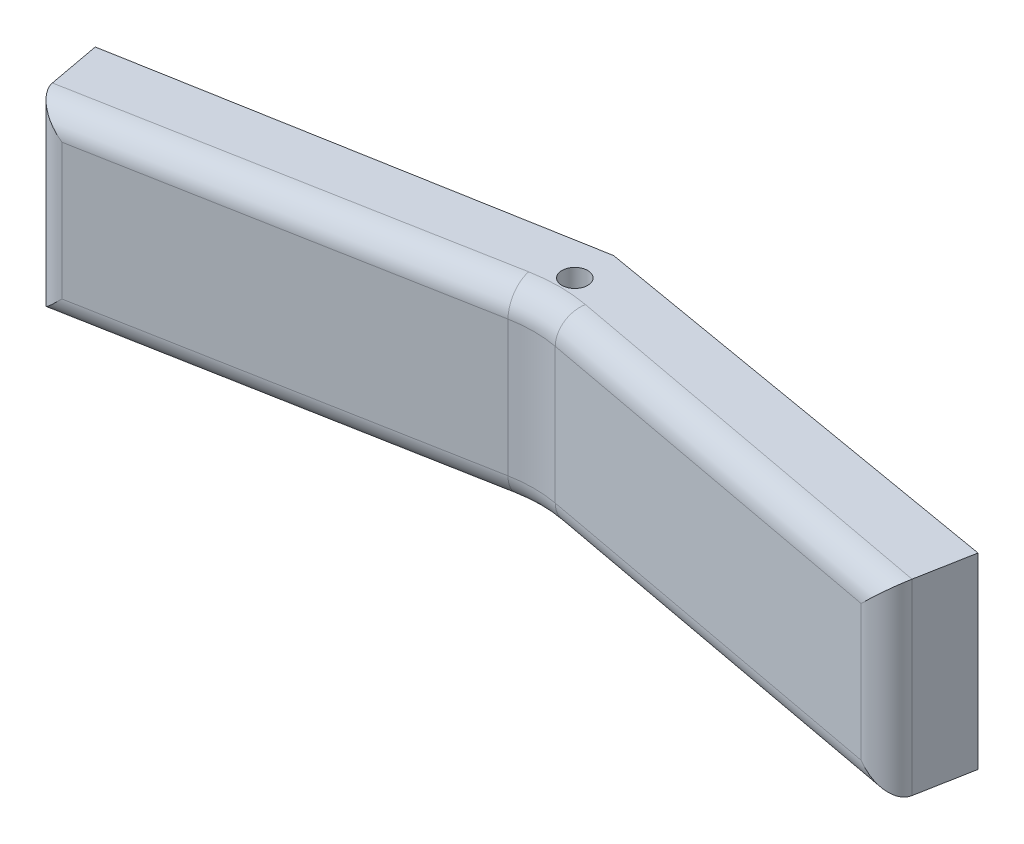
SolidWorks part; units mm, degrees
ref_plane "Plan de face" through (0, 0, 0) normal (0, 0, 1) x (1, 0, 0)
ref_plane "Plan de dessus" through (0, 0, 0) normal (0, 1, 0) x (1, 0, 0)
ref_plane "Plan de droite" through (0, 0, 0) normal (1, 0, 0) x (0, 0, -1)
sketch "Esquisse1" plane through (0, 0, 0) normal (0, 0, 1) x (1, 0, 0)
  line L0 (0, 0) -> (70, 0) construction
  line L1 (0, 0) -> (140, 0)
  line L2 (0, 0) -> (0, 30)
  line L3 (0, 30) -> (140, 30)
  line L4 (140, 0) -> (140, 30)
  line L5 (70, 0) -> (70, 30) construction
  dimension "D1" = 140
  dimension "D2" = 30
extrude "Boss.-Extru.1" add sketch "Esquisse1" along normal blind 20
sketch "Esquisse2" plane through (0, 0, 0) normal (0, -1, 0) x (1, 0, 0)
  line L0 (0, 0) -> (70, 0) construction
  line L1 (0, 0) -> (140, 0) construction
sketch "Esquisse3" plane through (0, 0, 20) normal (0, 0, 1) x (1, 0, 0)
  line L1 (0, 30) -> (140, 30)
  line L2 (0, 30) -> (0, 0)
  line L3 (0, 0) -> (140, 0)
  line L4 (140, 30) -> (140, 0)
extrude "Boss.-Extru.2" add sketch "Esquisse3" along normal blind 20
sketch "Esquisse4" plane through (0, 0, 0) normal (0, -1, 0) x (1, 0, 0)
  line L0 (70, 0) -> (70, 12) construction
  line L1 (0, 0) -> (0, 25) construction
  line L2 (0, 40) -> (0, 0) construction
  line L3 (0, 25) -> (140, 25) construction
  line L4 (140, 40) -> (140, 0) construction
  line L5 (70, 12) -> (0, 25)
  line L6 (70, 0) -> (0, 12.5)
  line L7 (0, 12.5) -> (0, 25)
  line L8 (70, 12) -> (70, 0)
sketch "Esquisse5" plane through (0, 0, 0) normal (0, -1, 0) x (1, 0, 0)
  line L0 (70, 12) -> (140, 25)
  line L1 (70, 0) -> (140, 12)
  line L2 (140, 40) -> (140, 0) construction
  line L3 (140, 12) -> (140, 25)
  line L4 (70, 12) -> (70, 0)
extrude "Boss.-Extru.3" add sketch "Esquisse5" along normal blind 30
sketch "Esquisse6" plane through (0, 0, 0) normal (0, -1, 0) x (1, 0, 0)
  line L0 (0, 25) -> (0, 12.5)
  line L1 (0, 12.5) -> (70, 0)
  line L2 (70, 0) -> (70, 12)
  line L3 (70, 12) -> (0, 25)
extrude "Boss.-Extru.4" add sketch "Esquisse6" along normal blind 30
sketch "Esquisse11" plane through (0, 0, 0) normal (-1, 0, 0) x (0, 0, 1)
  line L0 (12.5, 0) -> (25, 0)
sketch "Esquisse12" plane through (0, 0, 40) normal (0, 0, 1) x (1, 0, 0)
  line L1 (0, 30) -> (140, 30)
  line L2 (0, 30) -> (0, 0)
  line L3 (0, 0) -> (140, 0)
  line L4 (140, 30) -> (140, 0)
extrude "Enlèv. mat.-Extru.1" cut sketch "Esquisse12" against normal through all
sketch "Esquisse13" plane through (0, -30, 0) normal (0, -1, 0) x (1, 0, 0)
  line L0 (70, 12) -> (70, 0) construction
  circle A0 centre (70, 6) radius 2
extrude "Enlèv. mat.-Extru.2" cut sketch "Esquisse13" against normal through all
sketch "Esquisse14" plane through (2.1632, 0, 12.1137) normal (-0.1758, 0, -0.9844) x (-0.9844, 0, 0.1758)
  line L0 (-68.9099, -30) -> (-12.3099, -30) construction
  line L1 (2.1974, -30) -> (-68.9099, -30) construction
  line L2 (-12.3099, -30) -> (-12.3099, 0) construction
  line L3 (0, 0) -> (-68.9099, 0) construction
  circle A0 centre (-12.3099, -15) radius 2.5
  circle A1 centre (-12.3099, -15) radius 2.5
  circle A2 centre (-12.3099, -15) radius 2.5
sketch "Esquisse15" plane through (1.9984, 0, -11.6574) normal (0.169, 0, -0.9856) x (-0.9856, 0, -0.169)
  line L0 (-68.9936, -30) -> (-125.5936, -30) construction
  line L1 (-68.9936, -30) -> (-140.0147, -30) construction
  line L2 (-125.5936, -30) -> (-125.5936, 0) construction
  line L3 (-4.2241, 0) -> (-142.2112, 0) construction
  circle A0 centre (-125.5936, -15) radius 2.5
  circle A1 centre (-125.5936, -15) radius 2.5
sketch "Esquisse25" plane through (2.1632, 0, 12.1137) normal (-0.1758, 0, -0.9844) x (-0.9844, 0, 0.1758)
  circle A0 centre (-12.3099, -15) radius 2.5
extrude "Enlèv. mat.-Extru.11" cut sketch "Esquisse25" against normal blind 3
sketch "Esquisse16" plane through (0, 0, 0) normal (0, 1, 0) x (1, 0, 0)
  line L0 (0, -25) -> (8.7974, -23.3662) construction
  line L2 (70, -12) -> (0, -25) construction
  line L3 (8.7974, -23.3662) -> (6.6451, -11.3134) construction
  line L4 (70, 0) -> (0, -12.5) construction
  line L5 (6.6451, -11.3134) -> (0, -12.5) construction
  line L6 (0, -12.5) -> (2.244, -24.5833) construction
  line L7 (0, -12.5) -> (2.244, -24.5833)
  line L8 (2.244, -24.5833) -> (0, -25)
  line L9 (0, -25) -> (0, -12.5)
extrude "Enlèv. mat.-Extru.5" cut sketch "Esquisse16" against normal through all
sketch "Esquisse17" plane through (0, 0, 0) normal (0, 1, 0) x (1, 0, 0)
  line L0 (140, -25) -> (131.666, -23.4523) construction
  line L1 (140, -25) -> (70, -12) construction
  line L2 (131.666, -23.4523) -> (133.9844, -10.9688) construction
  line L3 (70, 0) -> (140, -12) construction
  line L4 (133.9844, -10.9688) -> (140, -12) construction
  line L5 (140, -12) -> (137.6662, -24.5666) construction
  line L6 (140, -12) -> (137.6662, -24.5666)
  line L7 (137.6662, -24.5666) -> (140, -25)
  line L8 (140, -25) -> (140, -12)
extrude "Enlèv. mat.-Extru.6" cut sketch "Esquisse17" against normal through all
sketch "Esquisse18" plane through (0, 0, 0) normal (0, 1, 0) x (1, 0, 0)
  line L0 (70, 0) -> (140, -12) construction
sketch "Esquisse19" plane through (137.4867, 0, 25.5332) normal (0.9832, 0, 0.1826) x (0.1826, 0, -0.9832)
  line L1 (0.9832, 0) -> (13.7646, 0)
  line L2 (0.9832, 0) -> (0.9832, -30)
  line L3 (0.9832, -30) -> (13.7646, -30)
  line L4 (13.7646, 0) -> (13.7646, -30)
extrude "Enlèv. mat.-Extru.7" cut sketch "Esquisse19" against normal blind 2
sketch "Esquisse20" plane through (-2.244, 0, 0.4167) normal (-0.9832, 0, 0.1826) x (0.1826, 0, 0.9832)
  line L1 (12.2899, 0) -> (24.5797, 0)
  line L2 (12.2899, 0) -> (12.2899, -30)
  line L3 (12.2899, -30) -> (24.5797, -30)
  line L4 (24.5797, 0) -> (24.5797, -30)
extrude "Enlèv. mat.-Extru.8" cut sketch "Esquisse20" against normal blind 2
sketch "Esquisse22" plane through (0, -30, 0) normal (0, -1, 0) x (1, 0, 0)
  line L0 (4.2104, 24.2181) -> (1.9689, 12.1484)
  line L1 (1.9689, 12.1484) -> (70, 0)
  line L2 (70, 0) -> (138.0286, 11.662)
  line L3 (138.0286, 11.662) -> (135.6998, 24.2014)
  line L4 (135.6998, 24.2014) -> (70, 12)
  line L5 (70, 12) -> (4.2104, 24.2181)
extrude "Enlèv. mat.-Extru.9" cut sketch "Esquisse22" against normal blind 0.5
sketch "Esquisse23" plane through (0, 0, 0) normal (0, 1, 0) x (1, 0, 0)
  line L0 (1.9689, -12.1484) -> (4.2104, -24.2181)
  line L1 (4.2104, -24.2181) -> (70, -12)
  line L2 (70, -12) -> (135.6998, -24.2014)
  line L3 (135.6998, -24.2014) -> (138.0286, -11.662)
  line L4 (138.0286, -11.662) -> (70, 0)
  line L5 (70, 0) -> (1.9689, -12.1484)
extrude "Enlèv. mat.-Extru.10" cut sketch "Esquisse23" against normal blind 0.5
sketch "Esquisse24" plane through (2.1632, 0, 12.1137) normal (-0.1758, 0, -0.9844) x (-0.9844, 0, 0.1758)
sketch "Esquisse26" plane through (2.1632, 0, 12.1137) normal (-0.1758, 0, -0.9844) x (-0.9844, 0, 0.1758)
extrude "Enlèv. mat.-Extru.15" cut sketch "Esquisse15" against normal blind 3 contours A1
fillet "Congé1" radius 20 1 edges at (70, -15, 12)
fillet "Congé3" radius 4 8 edges at (70, -29.5, 12.342) (35.2793, -29.5, 18.4481) (4.2104, -15, 24.2181) (35.2793, -0.5, 18.4481) (70, -0.5, 12.342) (104.6758, -29.5, 18.4398) (135.6998, -15, 24.2014) (104.6758, -0.5, 18.4398)
